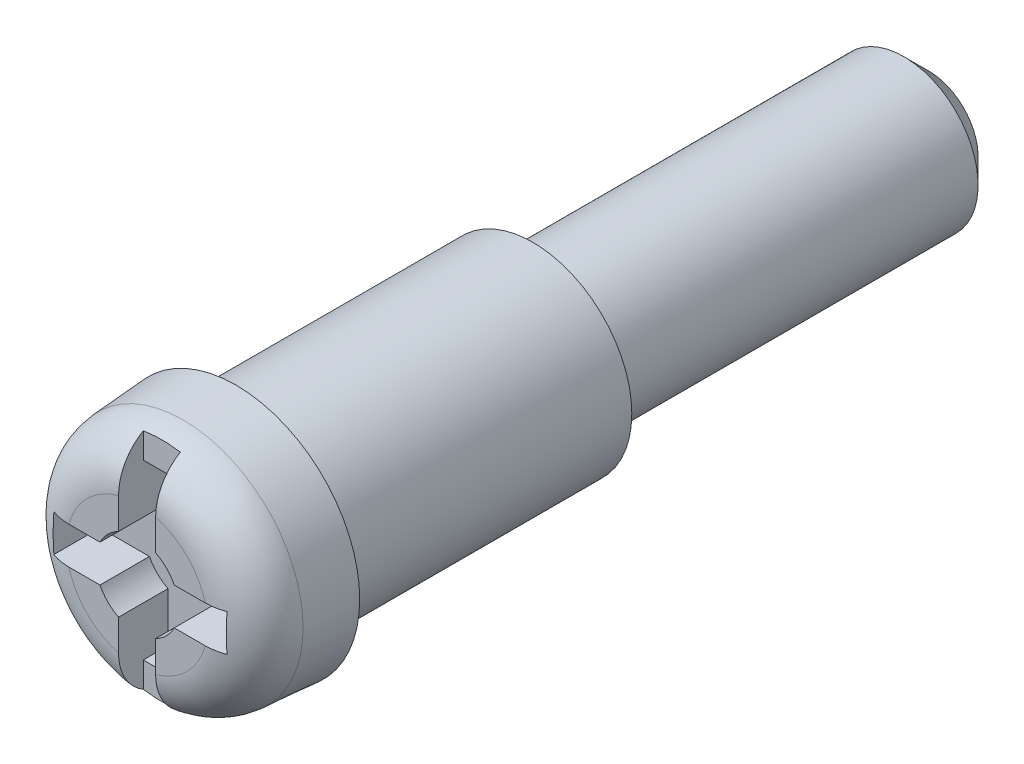
SolidWorks part; units mm, degrees
ref_plane "Plane1" through (0, 0, 0) normal (0, 0, 1) x (1, 0, 0)
ref_plane "Plane2" through (0, 0, 0) normal (0, 1, 0) x (1, 0, 0)
ref_plane "Plane3" through (0, 0, 0) normal (1, 0, 0) x (0, 0, -1)
sketch "Esquisse1" plane through (0, 0, 0) normal (0, 0, 1) x (1, 0, 0)
  circle A0 centre (0, 0) radius 2.5
  dimension "D1" = 5
extrude "Base-Extrusion" add sketch "Esquisse1" along normal blind 2 draft 4
fillet "Congé1" radius 1
sketch "Esquisse2" plane through (0, 0, 0) normal (0, 0, -1) x (-1, 0, 0)
  circle A0 centre (0, 0) radius 2
  dimension "D1" = 4
extrude "Boss.-Extru.1" add sketch "Esquisse2" along normal blind 6
sketch "Esquisse3" plane through (0, 0, -6) normal (0, 0, -1) x (-1, 0, 0)
  circle A0 centre (0, 0) radius 1.5
  dimension "D1" = 3
extrude "Boss.-Extru.2" add sketch "Esquisse3" along normal blind 8
chamfer "Chanfrein1" distance 0.5 angle 45
sketch "Esquisse4" plane through (0, 0, 2) normal (0, 0, 1) x (1, 0, 0)
  line L0 (0, 0) -> (-2, 0) construction
  line L1 (-1.75, -0.375) -> (-0.75, -0.375)
  line L2 (-1.75, 0.375) -> (-0.75, 0.375)
  line L3 (-1.75, -0.375) -> (-1.75, 0.375)
  line L4 (0.375, 1.75) -> (0.375, 0.75)
  line L5 (-0.375, 1.75) -> (0.375, 1.75)
  line L6 (-0.375, 1.75) -> (-0.375, 0.75)
  line L7 (1.75, -0.375) -> (0.75, -0.375)
  line L8 (1.75, 0.375) -> (1.75, -0.375)
  line L9 (1.75, 0.375) -> (0.75, 0.375)
  line L10 (-0.375, -1.75) -> (-0.375, -0.75)
  line L11 (0.375, -1.75) -> (-0.375, -1.75)
  line L12 (0.375, -1.75) -> (0.375, -0.75)
  arc A0 (0.375, -0.75) -> (0.75, -0.375) centre (0, 0) ccw
  arc A1 (-0.75, -0.375) -> (-0.375, -0.75) centre (0, 0) ccw
  arc A2 (-0.375, 0.75) -> (-0.75, 0.375) centre (0, 0) ccw
  arc A3 (0.75, 0.375) -> (0.375, 0.75) centre (0, 0) ccw
  dimension "D1" = 0.75
  dimension "D2" = 1
  dimension "D3" = 0.75
extrude "Enlèv. mat.-Extru.1" cut sketch "Esquisse4" against normal blind 1
sketch "Esquisse5" plane through (0, 0, 2) normal (0, 0, 1) x (1, 0, 0)
  line L1 (0.375, -3.0001) -> (-0.375, -3.0001)
  line L2 (0.375, -3.0001) -> (0.375, 2.5933)
  line L3 (0.375, 2.5933) -> (-0.375, 2.5933)
  line L4 (-0.375, -3.0001) -> (-0.375, 2.5933)
extrude "Enlèv. mat.-Extru.2" cut sketch "Esquisse5" against normal blind 0.5
